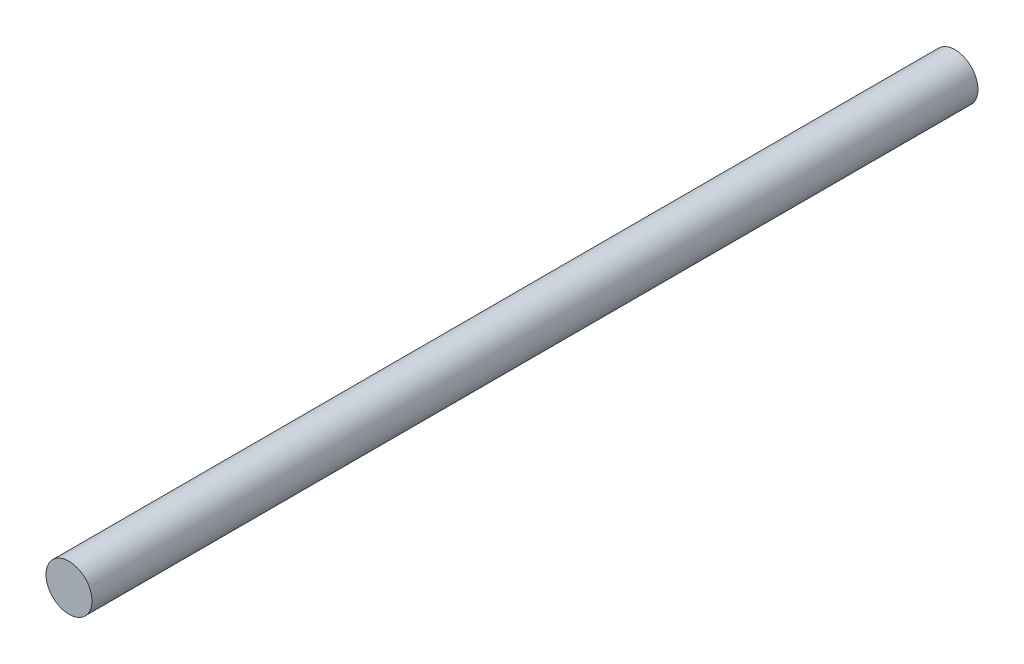
SolidWorks part; units mm, degrees
ref_plane "前视基准面" through (0, 0, 0) normal (0, 0, 1) x (1, 0, 0)
ref_plane "上视基准面" through (0, 0, 0) normal (0, 1, 0) x (1, 0, 0)
ref_plane "右视基准面" through (0, 0, 0) normal (1, 0, 0) x (0, 0, -1)
sketch "草图1" plane through (0, 0, 0) normal (0, 0, 1) x (1, 0, 0)
  circle A0 centre (0, 0) radius 4
  dimension "D1" = 8
extrude "凸台-拉伸1" add sketch "草图1" along normal blind 154
